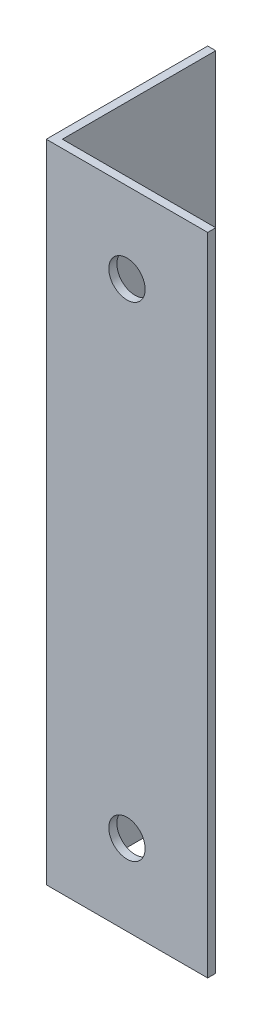
SolidWorks part; units mm, degrees
material "1060 Сплав"
ref_plane "Спереди" through (0, 0, 0) normal (0, 0, 1) x (1, 0, 0)
ref_plane "Сверху" through (0, 0, 0) normal (0, 1, 0) x (1, 0, 0)
ref_plane "Справа" through (0, 0, 0) normal (1, 0, 0) x (0, 0, -1)
sketch "Эскиз1" plane through (0, 0, 0) normal (0, 1, 0) x (1, 0, 0)
  line L0 (0, 0) -> (0, 20)
  line L1 (0, 20) -> (1, 20)
  line L2 (1, 20) -> (1, 1)
  line L3 (1, 1) -> (20, 1)
  line L4 (20, 1) -> (20, 0)
  line L5 (20, 0) -> (0, 0)
  dimension "D1" = 1
  dimension "D2" = 20
extrude "Бобышка-Вытянуть1" add sketch "Эскиз1" along normal blind 80
sketch "Эскиз2" plane through (0, 0, -1) normal (0, 0, -1) x (-1, 0, 0)
  line L0 (-20, 80) -> (-20, 0) construction
  line L3 (-20, 0) -> (-1, 0) construction
  line L4 (-20, 80) -> (-1, 80) construction
  circle A0 centre (-10, 10) radius 2.25
  circle A1 centre (-10, 70) radius 2.25
  dimension "D1" = 4.5
  dimension "D2" = 10
  dimension "D3" = 10
  dimension "D4" = 4.5
  dimension "D5" = 10
  dimension "D6" = 10
extrude "Вырез-Вытянуть1" cut sketch "Эскиз2" against normal through all
